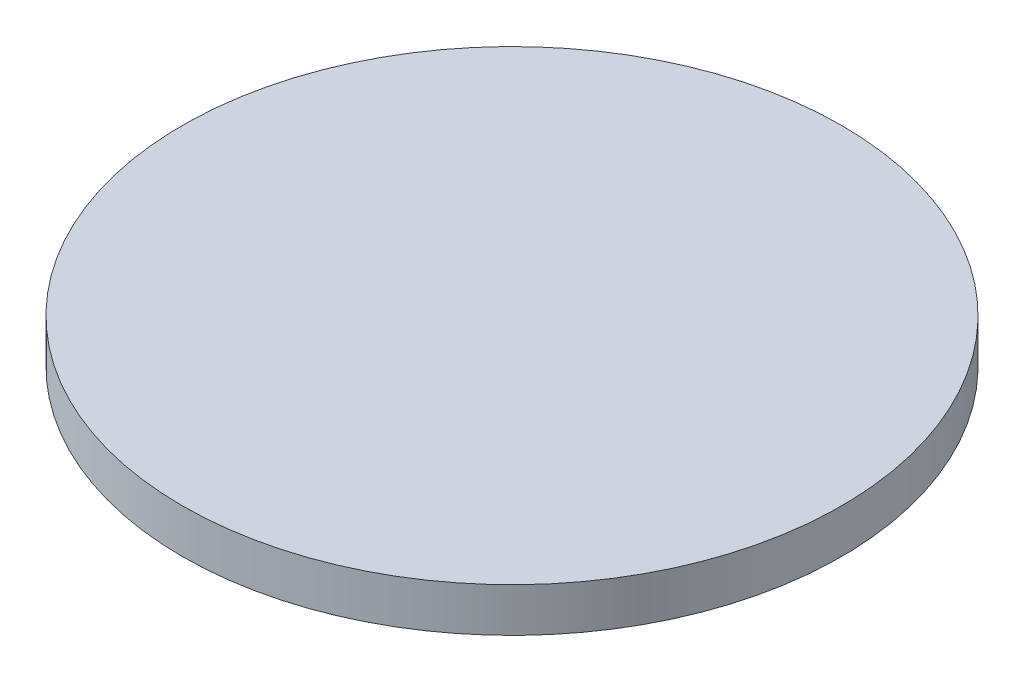
SolidWorks part; units mm, degrees
ref_plane "Face" through (0, 0, 0) normal (0, 0, 1) x (1, 0, 0)
ref_plane "Dessus" through (0, 0, 0) normal (0, 1, 0) x (1, 0, 0)
ref_plane "Droite" through (0, 0, 0) normal (1, 0, 0) x (0, 0, -1)
sketch "Esquisse1" plane through (0, 0, 0) normal (0, 1, 0) x (1, 0, 0)
  circle A0 centre (0, 0) radius 75
  dimension "D1" = 150
extrude "Extrusion1" add sketch "Esquisse1" along normal blind 10
